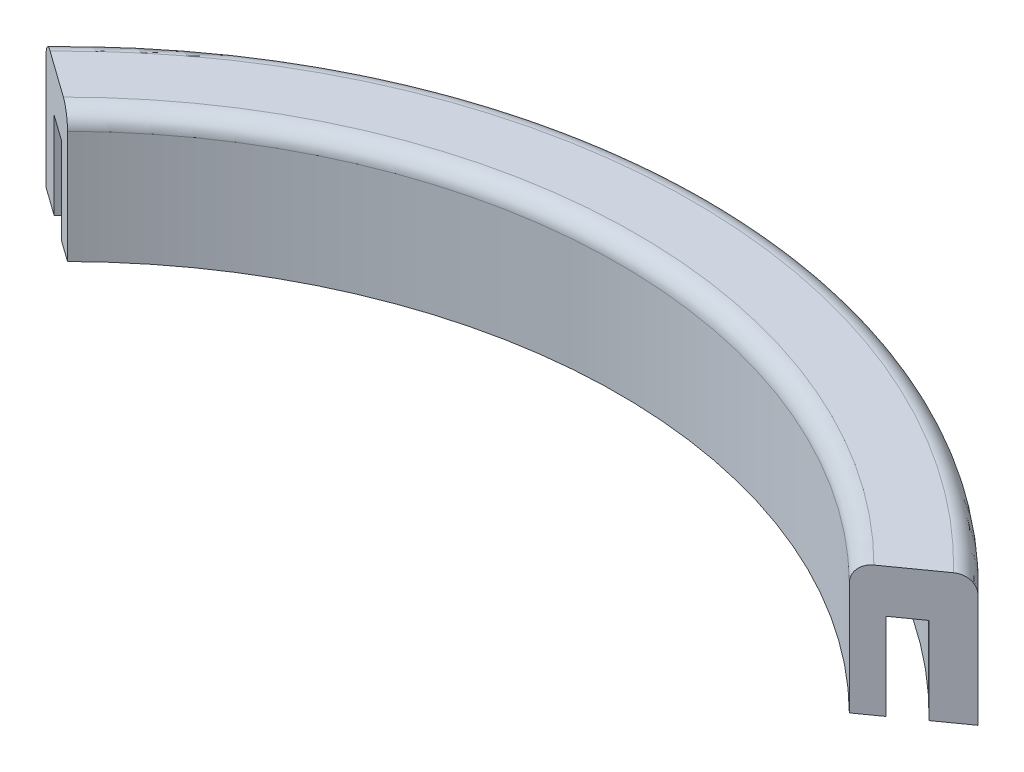
SolidWorks part; units mm, degrees
ref_plane "Front Plane" through (0, 0, 0) normal (0, 0, 1) x (1, 0, 0)
ref_plane "Top Plane" through (0, 0, 0) normal (0, 1, 0) x (1, 0, 0)
ref_plane "Right Plane" through (0, 0, 0) normal (1, 0, 0) x (0, 0, -1)
sketch "Sketch1" plane through (0, 0, 0) normal (0, 1, 0) x (1, 0, 0)
  line L0 (57.2347, 57.7116) -> (68.2256, 65.5535)
  line L1 (-57.2347, 57.7116) -> (-68.2256, 65.5535)
  line L2 (0, 0) -> (0, 94.615) construction
  arc A0 (-68.2256, 65.5535) -> (68.2256, 65.5535) centre (0, 0) cw
  arc A1 (-57.2347, 57.7116) -> (57.2347, 57.7116) centre (0, 0) cw
  dimension "D1" = 94.615
  dimension "D2" = 81.28
  dimension "D4" = 152.4
  dimension "D3" = 127
extrude "Boss-Extrude1" add sketch "Sketch1" along normal blind 19.05
sketch "Sketch3" plane through (0, 0, 0) normal (0, -1, 0) x (1, 0, 0)
  line L0 (-60.3794, -59.9553) -> (-64.0435, -62.5696)
  line L1 (64.0435, -62.5696) -> (60.3794, -59.9553)
  line L2 (57.2347, -57.7116) -> (68.2256, -65.5535) construction
  line L3 (-68.2256, -65.5535) -> (-57.2347, -57.7116) construction
  arc A0 (-64.0435, -62.5696) -> (64.0435, -62.5696) centre (0, 0) ccw
  arc A1 (-60.3794, -59.9553) -> (60.3794, -59.9553) centre (0, 0) ccw
  dimension "D1" = 89.535
  dimension "D2" = 85.09
extrude "Cut-Extrude1" cut sketch "Sketch3" against normal blind 12.7
fillet "Fillet1" radius 2.54 2 edges at (0, 19.05, -81.28) (0, 19.05, -94.615)
